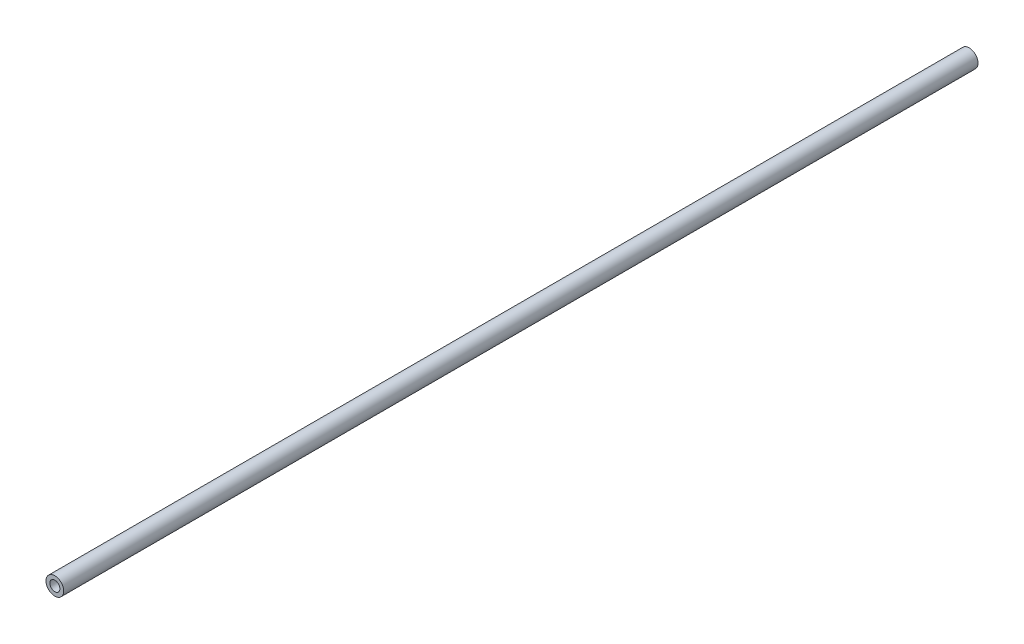
SolidWorks part; units mm, degrees
ref_plane "Alzado" through (0, 0, 0) normal (0, 0, 1) x (1, 0, 0)
ref_plane "Planta" through (0, 0, 0) normal (0, 1, 0) x (1, 0, 0)
ref_plane "Vista lateral" through (0, 0, 0) normal (1, 0, 0) x (0, 0, -1)
sketch "Croquis1" plane through (0, 0, 0) normal (0, 0, 1) x (1, 0, 0)
  circle A0 centre (0, 0) radius 6
  dimension "D1" = 12
extrude "Saliente-Extruir1" add sketch "Croquis1" along normal blind 620
hole_wizard "Taladro roscado M81" positions "Croquis2" profile "Croquis4" tap size "M8" standard "ISO"
sketch "Croquis2" plane through (0, 0, 620) normal (0, 0, 1) x (1, 0, 0)
  point P0 (0, 0)
sketch "Croquis4" plane through (0, 0, 620) normal (1, 0, 0) x (0, -1, 0)
  line L0 (0, 0) -> (0, 32.0429)
  line L1 (0, 32.0429) -> (3.4, 30)
  line L2 (3.4, 30) -> (3.4, 0)
  line L5 (3.4, 0) -> (0, 0)
  line L10 (0, 32.0429) -> (-3.4, 30) construction
  line L11 (0, -6.35) -> (0, 107.95) construction
  dimension "Diámetro de perforador para roscar" = 6.8
  dimension "Profundidad de perforador para roscar" = 30
  dimension "Ángulo de perforador" = 118
hole_wizard "Taladro roscado M82" positions "Croquis5" profile "Croquis6" tap size "M8" standard "ISO"
sketch "Croquis5" plane through (0, 0, 0) normal (0, 0, -1) x (-1, 0, 0)
  point P0 (0, 0)
sketch "Croquis6" plane through (0, 0, 0) normal (1, 0, 0) x (0, 1, 0)
  line L0 (0, 0) -> (0, 32.0429)
  line L1 (0, 32.0429) -> (3.4, 30)
  line L2 (3.4, 30) -> (3.4, 0)
  line L5 (3.4, 0) -> (0, 0)
  line L10 (0, 32.0429) -> (-3.4, 30) construction
  line L11 (0, -6.35) -> (0, 107.95) construction
  dimension "Diámetro de perforador para roscar" = 6.8
  dimension "Profundidad de perforador para roscar" = 30
  dimension "Ángulo de perforador" = 118
